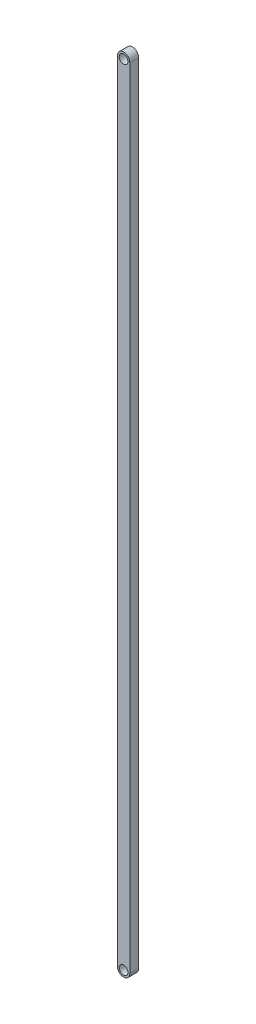
SolidWorks part; units mm, degrees
ref_plane "Front Plane" through (0, 0, 0) normal (0, 0, 1) x (1, 0, 0)
ref_plane "Top Plane" through (0, 0, 0) normal (0, 1, 0) x (1, 0, 0)
ref_plane "Right Plane" through (0, 0, 0) normal (1, 0, 0) x (0, 0, -1)
sketch "Sketch2" plane through (0, 0, 0) normal (0, 0, 1) x (1, 0, 0)
  line L0 (0, 0) -> (0, -448) construction
  line L1 (3.5, 0) -> (3.5, -448)
  line L2 (-3.5, 0) -> (-3.5, -448)
  arc A0 (3.5, 0) -> (-3.5, 0) centre (0, 0) ccw
  arc A1 (-3.5, -448) -> (3.5, -448) centre (0, -448) ccw
  circle A2 centre (0, 0) radius 2.5
  circle A3 centre (0, -448) radius 2.5
  point P3 (0, -224)
  dimension "D2" = 5
  dimension "D3" = 3.5
  dimension "D1" = 448
extrude "Boss-Extrude1" add sketch "Sketch2" along normal mid plane 5
